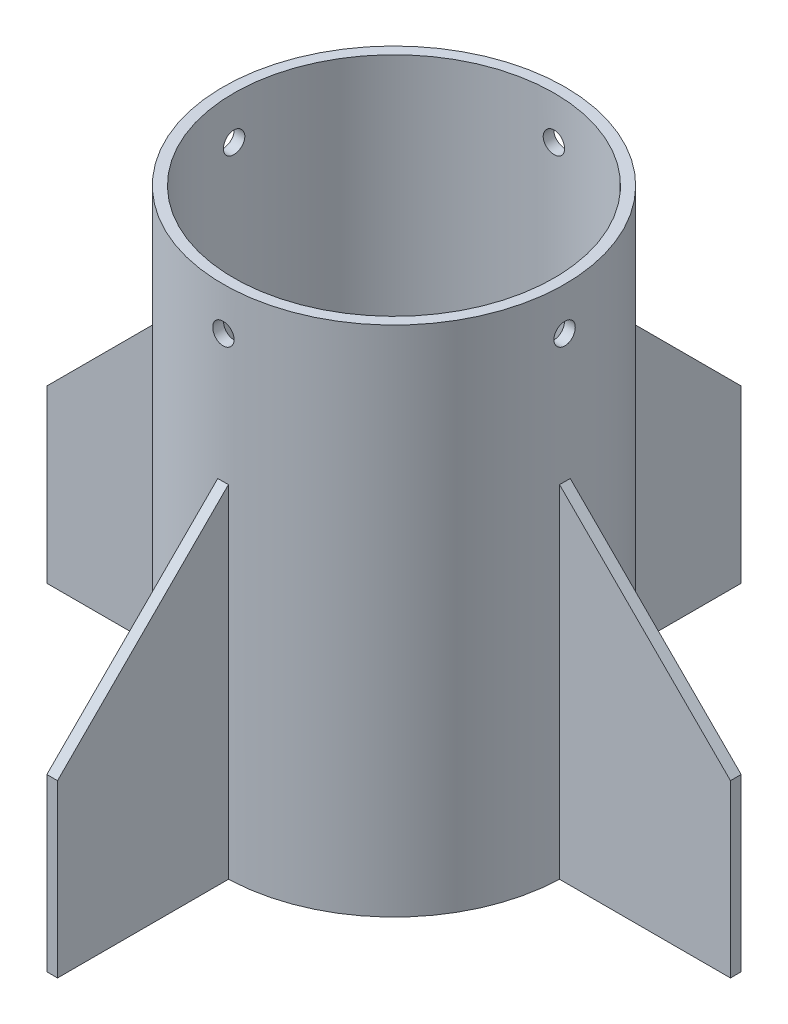
SolidWorks part; units mm, degrees
ref_plane "Front Plane" through (0, 0, 0) normal (0, 0, 1) x (1, 0, 0)
ref_plane "Top Plane" through (0, 0, 0) normal (0, 1, 0) x (1, 0, 0)
ref_plane "Right Plane" through (0, 0, 0) normal (1, 0, 0) x (0, 0, -1)
sketch "Sketch1" plane through (0, 0, 0) normal (0, 0, 1) x (1, 0, 0)
  line L0 (0, 0) -> (0, 203.2) construction
  line L1 (0, 0) -> (101.6, 0) construction
  line L4 (95.25, 6.35) -> (95.25, 304.8)
  line L5 (95.25, 304.8) -> (101.6, 304.8)
  line L6 (101.6, 0) -> (101.6, 304.8)
  line L7 (101.6, 0) -> (69.85, 0)
  line L9 (95.25, 6.35) -> (69.85, 6.35)
  line L10 (69.85, 0) -> (69.85, 6.35)
  dimension "D2" = 25.4
  dimension "D3" = 6.35
  dimension "D4" = 101.6
  dimension "D5" = 6.35
  dimension "D6" = 304.8
revolve "Revolve1" add sketch "Sketch1" angle 360 about L0
sketch "Sketch2" plane through (0, 0, 0) normal (0, -1, 0) x (1, 0, 0)
  circle A2 centre (0, 82.55) radius 6.35
  circle A3 centre (41.275, 71.4904) radius 6.35
  circle A4 centre (71.4904, 41.275) radius 6.35
  circle A5 centre (82.55, 0) radius 6.35
  circle A6 centre (71.4904, -41.275) radius 6.35
  circle A7 centre (41.275, -71.4904) radius 6.35
  circle A8 centre (0, -82.55) radius 6.35
  circle A9 centre (-41.275, -71.4904) radius 6.35
  circle A10 centre (-71.4904, -41.275) radius 6.35
  circle A11 centre (-82.55, 0) radius 6.35
  circle A12 centre (-71.4904, 41.275) radius 6.35
  circle A13 centre (-41.275, 71.4904) radius 6.35
  point P30 (0, 0)
  dimension "D1" = 12
extrude "Cut-Extrude1" cut sketch "Sketch2" against normal through all
sketch "Sketch3" plane through (0, 0, 0) normal (0, 0, 1) x (1, 0, 0)
  line L0 (-101.6, 0) -> (-203.2, 0)
  line L1 (-203.2, 0) -> (-203.2, 101.6)
  line L2 (-203.2, 101.6) -> (-101.6, 203.2)
  line L3 (-101.6, 203.2) -> (-101.6, 0)
  line L4 (0, 0) -> (0, 304.8) construction
  line L5 (101.6, 304.8) -> (-101.6, 304.8) construction
  line L6 (203.2, 101.6) -> (101.6, 203.2)
  line L7 (203.2, 0) -> (203.2, 101.6)
  line L8 (101.6, 0) -> (203.2, 0)
  line L9 (101.6, 203.2) -> (101.6, 0)
  dimension "D1" = 101.6
  dimension "D2" = 101.6
  dimension "D3" = 203.2
extrude "Boss-Extrude1" add sketch "Sketch3" along normal mid plane 6.35 separate body
sketch "Sketch4" plane through (0, 0, 0) normal (1, 0, 0) x (0, 0, -1)
  line L0 (-101.6, 0) -> (-203.2, 0)
  line L1 (-203.2, 0) -> (-203.2, 101.6)
  line L2 (-203.2, 101.6) -> (-101.6, 203.2)
  line L3 (-101.6, 203.2) -> (-101.6, 0)
  line L4 (0, 0) -> (0, 152.4) construction
  line L5 (203.2, 101.6) -> (101.6, 203.2)
  line L6 (203.2, 0) -> (203.2, 101.6)
  line L7 (101.6, 0) -> (203.2, 0)
  line L8 (101.6, 203.2) -> (101.6, 0)
  line L9 (-101.6, 0) -> (101.6, 0) construction
  point P10 (0, 0)
  point P11 (0, 0)
  point P13 (0, 0)
  point P14 (0, 0)
  point P15 (0, 0)
  point P16 (0, 0)
  point P17 (0, 0)
  point P18 (0, 0)
  dimension "D1" = 101.6
  dimension "D2" = 101.6
  dimension "D3" = 203.2
extrude "Boss-Extrude3" add sketch "Sketch4" along normal mid plane 6.35 separate body
sketch "Sketch5" plane through (0, 0, 0) normal (0, 0, 1) x (1, 0, 0)
  line L0 (0, 304.8) -> (0, 279.4) construction
  line L1 (101.6, 304.8) -> (-101.6, 304.8) construction
  circle A0 centre (0, 279.4) radius 6.35
  dimension "D2" = 12.7
  dimension "D1" = 25.4
extrude "Cut-Extrude2" cut sketch "Sketch5" against normal through all both and the other way through all
sketch "Sketch6" plane through (0, 0, 0) normal (1, 0, 0) x (0, 0, -1)
  line L0 (0, 304.8) -> (0, 279.4) construction
  line L1 (101.6, 304.8) -> (-101.6, 304.8) construction
  circle A0 centre (0, 279.4) radius 6.35
  dimension "D2" = 12.7
  dimension "D1" = 25.4
extrude "Cut-Extrude3" cut sketch "Sketch6" against normal through all both and the other way through all
